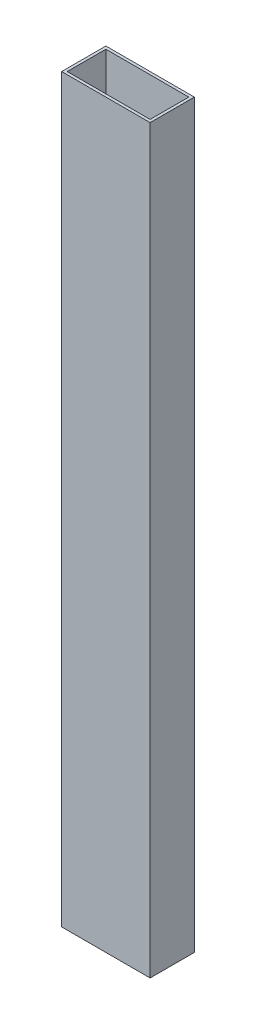
SolidWorks part; units mm, degrees
ref_plane "Front Plane" through (0, 0, 0) normal (0, 0, 1) x (1, 0, 0)
ref_plane "Top Plane" through (0, 0, 0) normal (0, 1, 0) x (1, 0, 0)
ref_plane "Right Plane" through (0, 0, 0) normal (1, 0, 0) x (0, 0, -1)
sketch "Sketch1" plane through (0, 0, 0) normal (0, 1, 0) x (1, 0, 0)
  line L1 (-49.2125, 23.8125) -> (1.5875, 23.8125)
  line L2 (-49.2125, 23.8125) -> (-49.2125, -1.5875)
  line L3 (-49.2125, -1.5875) -> (1.5875, -1.5875)
  line L4 (1.5875, 23.8125) -> (1.5875, -1.5875)
  line L5 (-47.625, 22.225) -> (0, 22.225)
  line L6 (-47.625, 22.225) -> (-47.625, 0)
  line L7 (-47.625, 0) -> (0, 0)
  line L8 (0, 22.225) -> (0, 0)
  dimension "D1" = 50.8
  dimension "D2" = 25.4
  dimension "D3" = 1.5875
  dimension "D4" = 1.5875
  dimension "D5" = 1.5875
  dimension "D6" = 1.5875
extrude "Boss-Extrude1" add sketch "Sketch1" along normal blind 425.45
